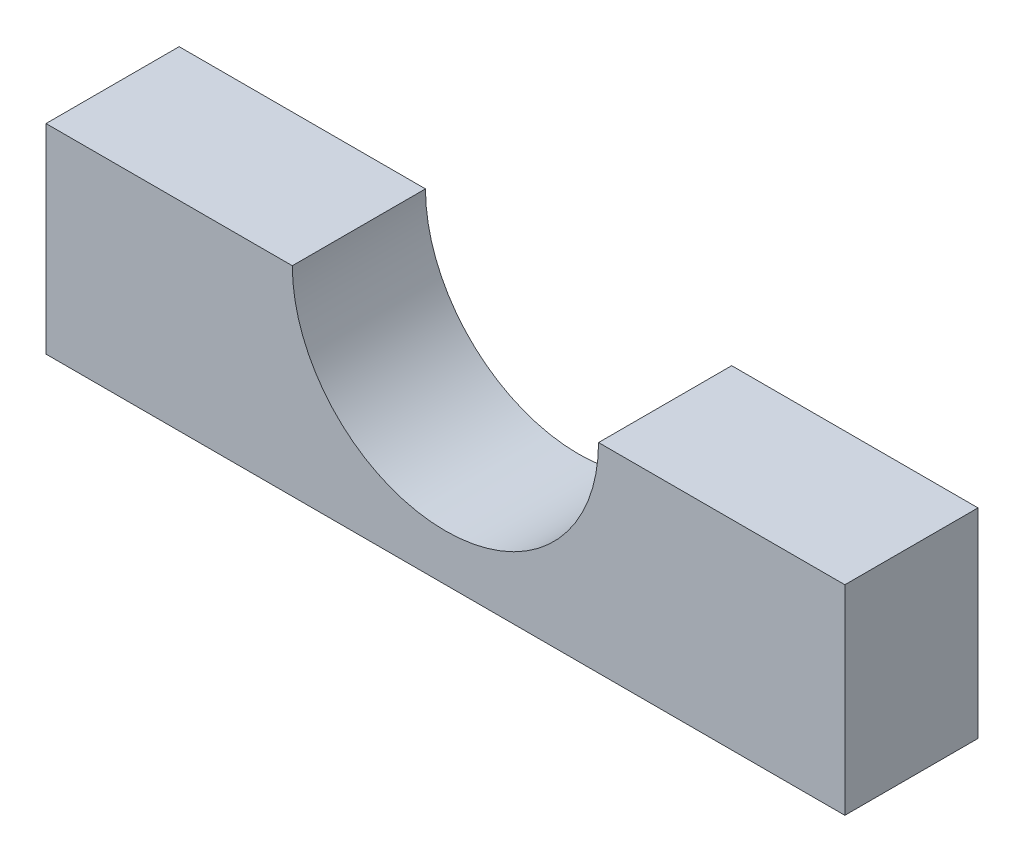
SolidWorks part; units mm, degrees
ref_plane "Front Plane" through (0, 0, 0) normal (0, 0, 1) x (1, 0, 0)
ref_plane "Top Plane" through (0, 0, 0) normal (0, 1, 0) x (1, 0, 0)
ref_plane "Right Plane" through (0, 0, 0) normal (1, 0, 0) x (0, 0, -1)
sketch "Sketch1" plane through (0, 0, 0) normal (0, 0, 1) x (1, 0, 0)
  line L1 (-38.1, -19.05) -> (38.1, -19.05)
  line L3 (-14.605, 0) -> (-38.1, 0)
  line L4 (14.605, 0) -> (38.1, 0)
  line L5 (38.1, 0) -> (38.1, -19.05)
  line L6 (-38.1, 0) -> (-38.1, -19.05)
  line L7 (0, -19.05) -> (0, 0) construction
  circle A0 centre (0, 0) radius 14.605 construction
  arc A1 (-14.605, 0) -> (14.605, 0) centre (0, 0) ccw
  dimension "D1" = 29.21
  dimension "D3" = 76.2
  dimension "D2" = 19.05
extrude "Boss-Extrude1" add sketch "Sketch1" along normal blind 12.7
